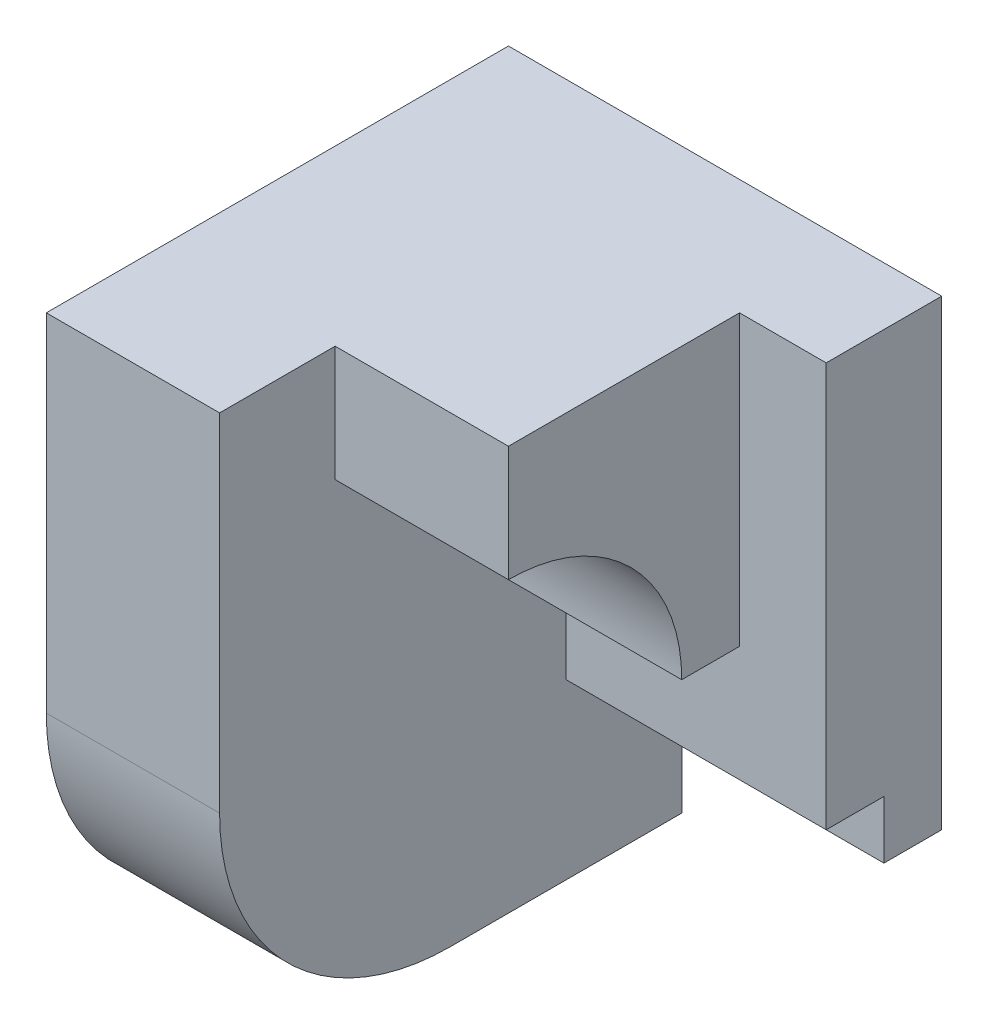
SolidWorks part; units mm, degrees
ref_plane "Front" through (0, 0, 0) normal (0, 0, 1) x (1, 0, 0)
ref_plane "Top" through (0, 0, 0) normal (0, 1, 0) x (1, 0, 0)
ref_plane "Right" through (0, 0, 0) normal (1, 0, 0) x (0, 0, -1)
sketch "Sketch1" plane through (0, 0, 0) normal (1, 0, 0) x (0, 0, -1)
  line L1 (4, -5) -> (0, -5)
  line L2 (4, -5) -> (4, 5)
  line L3 (4, 5) -> (-4, 5)
  line L4 (-4, -1) -> (-4, 5)
  line L5 (4, -5) -> (-4, 5) construction
  line L6 (4, 5) -> (-4, -5) construction
  arc A0 (0, -5) -> (-4, -1) centre (0, -1) cw
  point P0 (0, 0)
  dimension "D3" = 4
  dimension "D1" = 8
  dimension "D2" = 10
extrude "Boss-Extrude1" add sketch "Sketch1" along normal blind 3
sketch "Sketch2" plane through (3, 0, 0) normal (1, 0, 0) x (0, 0, -1)
  line L1 (4, 5) -> (2, 5)
  line L2 (4, 5) -> (4, -3)
  line L3 (4, -3) -> (2, -3)
  line L4 (2, 5) -> (2, -3)
  line L5 (2, -3) -> (3, -3)
  line L6 (2, -3) -> (2, -2)
  line L7 (2, -2) -> (3, -2)
  line L8 (3, -3) -> (3, -2)
  line M8 (4, -5) -> (4, 5)
  line M9 (4, 5) -> (-4, 5)
  dimension "D1" = 8
  dimension "D2" = 2
  dimension "D3" = 1
  dimension "D4" = 1
extrude "Boss-Extrude2" add sketch "Sketch2" along normal blind 4.5 contours L8 L3 L4 L7 M8 M9
sketch "Sketch3" plane through (3, 0, 0) normal (1, 0, 0) x (0, 0, -1)
  line L1 (2, 5) -> (-2, 5)
  line L2 (2, 5) -> (2, 0)
  line L3 (2, 0) -> (-2, 0)
  line L4 (-2, 5) -> (-2, 0)
  circle A0 centre (-2, 0) radius 3
  line M3 (2, -2) -> (2, 5)
  line M4 (2, 5) -> (-4, 5)
  dimension "D1" = 5
  dimension "D2" = 4
extrude "Boss-Extrude3" add sketch "Sketch3" along normal blind 3 contours A0 L3 L4 M3 M4
